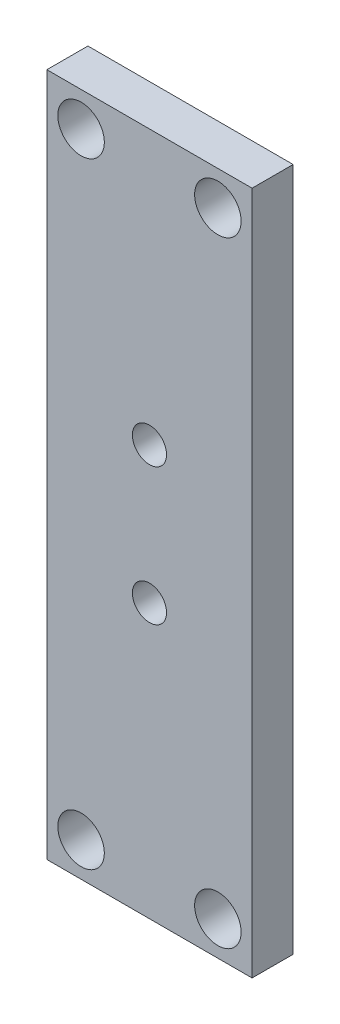
SolidWorks part; units mm, degrees
ref_plane "정면" through (0, 0, 0) normal (0, 0, 1) x (1, 0, 0)
ref_plane "윗면" through (0, 0, 0) normal (0, 1, 0) x (1, 0, 0)
ref_plane "우측면" through (0, 0, 0) normal (1, 0, 0) x (0, 0, -1)
sketch "스케치1" plane through (0, 0, 0) normal (0, 0, 1) x (1, 0, 0)
  line L0 (0, 0) -> (-13.1641, 0) construction
  line L1 (-7.5, 25) -> (7.5, 25)
  line L2 (-7.5, 25) -> (-7.5, -25)
  line L3 (-7.5, -25) -> (7.5, -25)
  line L4 (7.5, 25) -> (7.5, -25)
  line L5 (-7.5, 25) -> (7.5, -25) construction
  line L6 (-7.5, -25) -> (7.5, 25) construction
  point P0 (0, 0)
  dimension "D1" = 15
  dimension "D2" = 50
extrude "보스-돌출1" add sketch "스케치1" along normal blind 3
sketch "스케치2" plane through (0, 0, 0) normal (0, 0, -1) x (-1, 0, 0)
  line L0 (7.5, 25) -> (7.5, -25) construction
  line L1 (-7.5, 25) -> (7.5, 25)
  line L2 (-7.5, 25) -> (-7.5, 20)
  line L3 (-7.5, 20) -> (7.5, 20)
  line L4 (7.5, 25) -> (7.5, 20)
  line L5 (-7.5, 25) -> (7.5, 20) construction
  line L6 (-7.5, 20) -> (7.5, 25) construction
  line L7 (-7.5, 25) -> (7.5, 25) construction
  line L9 (0, 0) -> (13.4402, 0) construction
  line L10 (-7.5, -20) -> (7.5, -25) construction
  line L11 (-7.5, -25) -> (7.5, -20) construction
  line L12 (7.5, -25) -> (7.5, -20)
  line L13 (-7.5, -20) -> (7.5, -20)
  line L14 (-7.5, -25) -> (-7.5, -20)
  line L15 (-7.5, -25) -> (7.5, -25)
  line L23 (0, 0) -> (0, 6.6313) construction
  point P0 (0, 22.5)
  point P19 (0, -22.5)
  dimension "D1" = 5
extrude "보스-돌출2" [suppressed] add sketch "스케치2" along normal blind 12
sketch "스케치3" [suppressed] plane through (0, 0, -12) normal (0, 0, -1) x (-1, 0, 0)
  line L0 (0, 0) -> (0, 9.7101) construction
  line L1 (-7.5, 25) -> (7.5, 25)
  line L2 (-7.5, 25) -> (-7.5, -25)
  line L3 (-7.5, -25) -> (7.5, -25)
  line L4 (7.5, 25) -> (7.5, -25)
  line L5 (-7.5, 25) -> (7.5, -25) construction
  line L6 (-7.5, -25) -> (7.5, 25) construction
  line L7 (-5.5, 20) -> (-1.5, 20)
  line L8 (-5.5, 20) -> (-5.5, -20)
  line L9 (-5.5, -20) -> (-1.5, -20)
  line L10 (-1.5, 20) -> (-1.5, -20)
  line L17 (5.5, -20) -> (1.5, -20)
  line L18 (5.5, 20) -> (5.5, -20)
  line L19 (5.5, 20) -> (1.5, 20)
  line L20 (1.5, 20) -> (1.5, -20)
  line L21 (0, 0) -> (18.5385, 0) construction
  point P0 (0, 0)
  point P7 (0, 0)
  dimension "D1" = 40
  dimension "D2" = 1.5
  dimension "D3" = 4
extrude "보스-돌출3" [suppressed] add sketch "스케치3" along normal blind 3
sketch "스케치5" [suppressed] plane through (0, 0, -15) normal (0, 0, -1) x (-1, 0, 0)
  line L0 (-7.5, 16) -> (-10.5, 16)
  line L2 (-10.5, 16) -> (-10.5, 18)
  line L3 (-10.5, 18) -> (-13.5, 18)
  line L4 (-13.5, 18) -> (-13.5, 10)
  line L5 (-13.5, 10) -> (-10.5, 10)
  line L6 (-10.5, 10) -> (-10.5, 12)
  line L7 (-10.5, 12) -> (-7.5, 12)
  line L8 (-7.5, 16) -> (-7.5, 12)
  line L9 (-7.5, 14) -> (-13.1442, 14) construction
  line L11 (0, 0) -> (0, 7.6378) construction
  line L12 (0, 0) -> (17.2492, 0) construction
  line L13 (7.5, 14) -> (13.1442, 14) construction
  line L14 (7.5, 16) -> (7.5, 12)
  line L15 (10.5, 12) -> (7.5, 12)
  line L16 (10.5, 10) -> (10.5, 12)
  line L17 (13.5, 10) -> (10.5, 10)
  line L18 (13.5, 18) -> (13.5, 10)
  line L19 (10.5, 18) -> (13.5, 18)
  line L20 (10.5, 16) -> (10.5, 18)
  line L21 (7.5, 16) -> (10.5, 16)
  line L22 (7.5, -14) -> (13.1442, -14) construction
  line L23 (-7.5, -14) -> (-13.1442, -14) construction
  line L24 (7.5, -16) -> (10.5, -16)
  line L25 (10.5, -16) -> (10.5, -18)
  line L26 (10.5, -18) -> (13.5, -18)
  line L27 (13.5, -18) -> (13.5, -10)
  line L28 (13.5, -10) -> (10.5, -10)
  line L29 (10.5, -10) -> (10.5, -12)
  line L30 (10.5, -12) -> (7.5, -12)
  line L31 (7.5, -16) -> (7.5, -12)
  line L32 (-7.5, -16) -> (-7.5, -12)
  line L33 (-10.5, -12) -> (-7.5, -12)
  line L34 (-10.5, -10) -> (-10.5, -12)
  line L35 (-13.5, -10) -> (-10.5, -10)
  line L36 (-13.5, -18) -> (-13.5, -10)
  line L37 (-10.5, -18) -> (-13.5, -18)
  line L38 (-10.5, -16) -> (-10.5, -18)
  line L39 (-7.5, -16) -> (-10.5, -16)
  line L40 (-7.5, -25) -> (-7.5, 25) construction
  dimension "D1" = 8
  dimension "D2" = 4
  dimension "D3" = 10
  dimension "D4" = 3
  dimension "D5" = 3
extrude "보스-돌출4" [suppressed] add sketch "스케치5" against normal blind 3
hole_wizard "M3 나사 구멍1" positions "스케치6" profile "스케치7" tap size "M3" standard "ISO" end condition up to next
sketch "스케치6" plane through (0, 0, 3) normal (0, 0, 1) x (1, 0, 0)
  line L0 (7.5, 25) -> (-7.5, 25) construction
  point P0 (0, 5)
  point P2 (0, -5)
  dimension "D1" = 10
  dimension "D2" = 20
sketch "스케치7" plane through (0, 5, 3) normal (1, 0, 0) x (0, -1, 0)
  line L0 (0, 0) -> (0, 3)
  line L1 (0, 3) -> (1.25, 3)
  line L2 (1.25, 3) -> (1.25, 0)
  line L5 (1.25, 0) -> (0, 0)
  line L11 (0, -6.35) -> (0, 107.95) construction
  dimension "관통 탭 드릴 지름" = 2.5
  dimension "관통 탭 드릴 깊이" = 3
cosmetic thread "구멍 나사산1" parameters "D2"=3
cosmetic thread "구멍 나사산2" parameters "D2"=3
hole_wizard "M3 여유 구멍1" positions "스케치8" profile "스케치9" hole size "M3" standard "ISO" end condition through all
sketch "스케치8" plane through (0, 0, 3) normal (0, 0, 1) x (1, 0, 0)
  line L0 (7.5, 25) -> (-7.5, 25) construction
  line L1 (-7.5, 25) -> (-7.5, -25) construction
  line L2 (0, 0) -> (0, 11.73) construction
  line L3 (0, -1.65) -> (0, 1.65) construction
  line L5 (0, 0) -> (19.1877, 0) construction
  point P0 (-5, 22.5)
  point P2 (5, 22.5)
  point P20 (0, 0)
  point P21 (0, 0)
  point P22 (-5, -22.5)
  point P23 (5, -22.5)
  dimension "D1" = 2.5
  dimension "D2" = 2.5
sketch "스케치9" plane through (-5, 22.5, 3) normal (1, 0, 0) x (0, -1, 0)
  line L0 (0, 0) -> (0, 3)
  line L1 (0, 3) -> (1.7, 3)
  line L2 (1.7, 3) -> (1.7, 0)
  line L5 (1.7, 0) -> (0, 0)
  line L11 (0, -6.35) -> (0, 107.95) construction
  dimension "관통 구멍 지름" = 3.4
  dimension "관통 구멍 깊이" = 3
